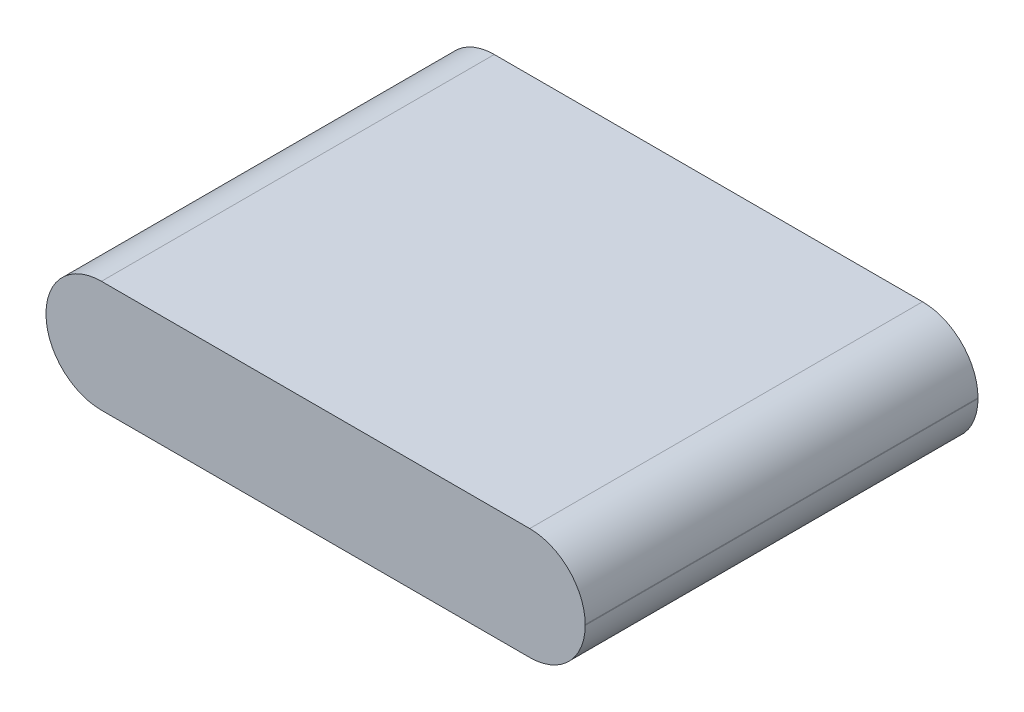
SolidWorks part; units mm, degrees
ref_plane "Front Plane" through (0, 0, 0) normal (0, 0, 1) x (1, 0, 0)
ref_plane "Top Plane" through (0, 0, 0) normal (0, 1, 0) x (1, 0, 0)
ref_plane "Right Plane" through (0, 0, 0) normal (1, 0, 0) x (0, 0, -1)
sketch "Sketch1" plane through (0, 0, 0) normal (0, 1, 0) x (1, 0, 0)
  line L1 (-35, -25.5) -> (35, -25.5)
  line L2 (-35, -25.5) -> (-35, 25.5)
  line L3 (-35, 25.5) -> (35, 25.5)
  line L4 (35, -25.5) -> (35, 25.5)
  line L5 (-35, -25.5) -> (35, 25.5) construction
  line L6 (-35, 25.5) -> (35, -25.5) construction
  point P0 (0, 0)
  dimension "D1" = 51
  dimension "D2" = 70
extrude "Boss-Extrude1" add sketch "Sketch1" along normal blind 14.5
fillet "Fillet1" radius 7.2 4 edges at (-35, 0, 0) (-35, 14.5, 0) (35, 0, 0) (35, 14.5, 0)
